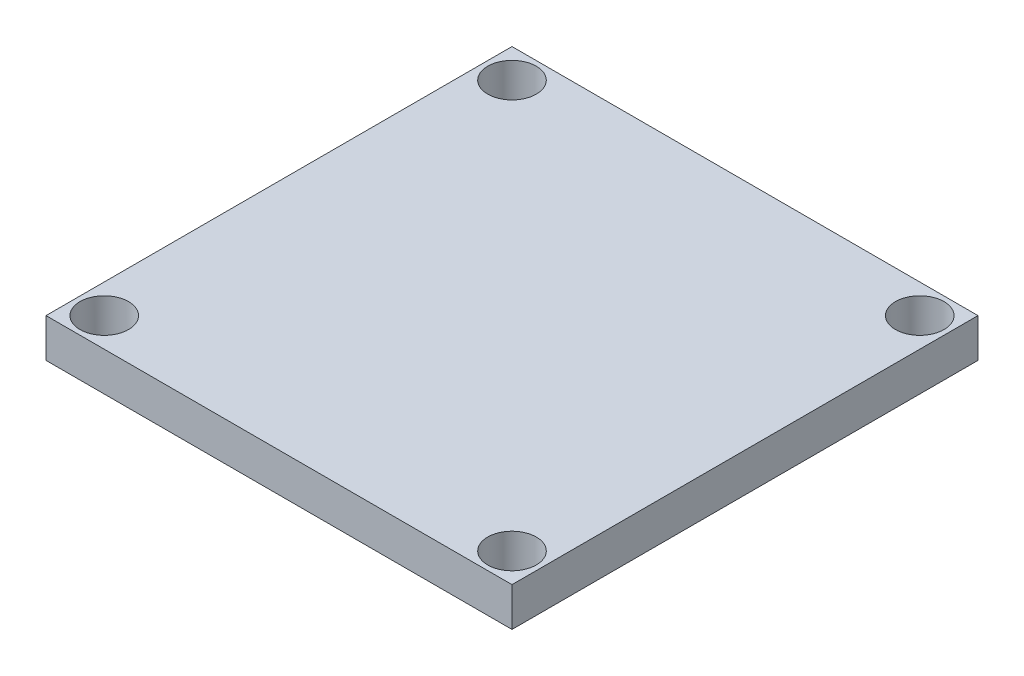
SolidWorks part; units mm, degrees
ref_plane "Front Plane" through (0, 0, 0) normal (0, 0, 1) x (1, 0, 0)
ref_plane "Top Plane" through (0, 0, 0) normal (0, 1, 0) x (1, 0, 0)
ref_plane "Right Plane" through (0, 0, 0) normal (1, 0, 0) x (0, 0, -1)
sketch "Sketch2" plane through (0, 0, 0) normal (0, 1, 0) x (1, 0, 0)
  line L1 (12, -12) -> (-12, -12)
  line L2 (12, -12) -> (12, 12)
  line L3 (12, 12) -> (-12, 12)
  line L4 (-12, -12) -> (-12, 12)
  line L5 (12, -12) -> (-12, 12) construction
  line L6 (12, 12) -> (-12, -12) construction
  point P0 (0, 0)
  dimension "D1" = 24
extrude "Boss-Extrude1" add sketch "Sketch2" along normal blind 2
sketch "Sketch3" plane through (0, 2, 0) normal (0, 1, 0) x (1, 0, 0)
  line L0 (12, 0) -> (-12, 0) construction
  line L1 (-12, 12) -> (-12, -12) construction
  line L2 (0, -12) -> (0, 12) construction
  line L3 (12, 12) -> (-12, 12) construction
  circle A0 centre (-10.5, 10.5) radius 1.25
  circle A1 centre (10.5, 10.5) radius 1.25
  circle A2 centre (10.5, -10.5) radius 1.25
  circle A3 centre (-10.5, -10.5) radius 1.25
  point P6 (0, 0)
  point P12 (0, 0)
  point P14 (-10.0911, 10.5383)
  dimension "D1" = 2.5
  dimension "D2" = 1.5
  dimension "D3" = 1.5
extrude "Cut-Extrude1" cut sketch "Sketch3" against normal up to surface (2 mm away) up to face at (0, 0, 0)
